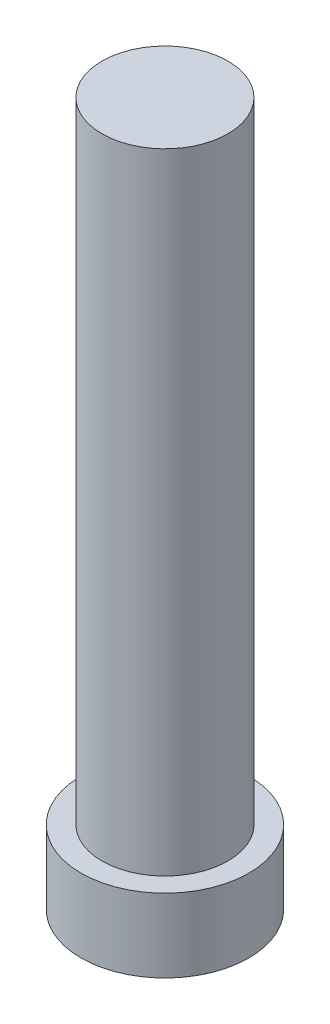
SolidWorks part; units mm, degrees
ref_plane "Front Plane" through (0, 0, 0) normal (0, 0, 1) x (1, 0, 0)
ref_plane "Top Plane" through (0, 0, 0) normal (0, 1, 0) x (1, 0, 0)
ref_plane "Right Plane" through (0, 0, 0) normal (1, 0, 0) x (0, 0, -1)
sketch "Sketch1" plane through (0, 0, 0) normal (0, 1, 0) x (1, 0, 0)
  circle A0 centre (0, 0) radius 8
extrude "Boss-Extrude1" add sketch "Sketch1" along normal mid plane 7
sketch "Sketch2" plane through (0, 3.5, 0) normal (0, 1, 0) x (1, 0, 0)
  circle A0 centre (0, 0) radius 6
extrude "Boss-Extrude2" add sketch "Sketch2" along normal blind 60
